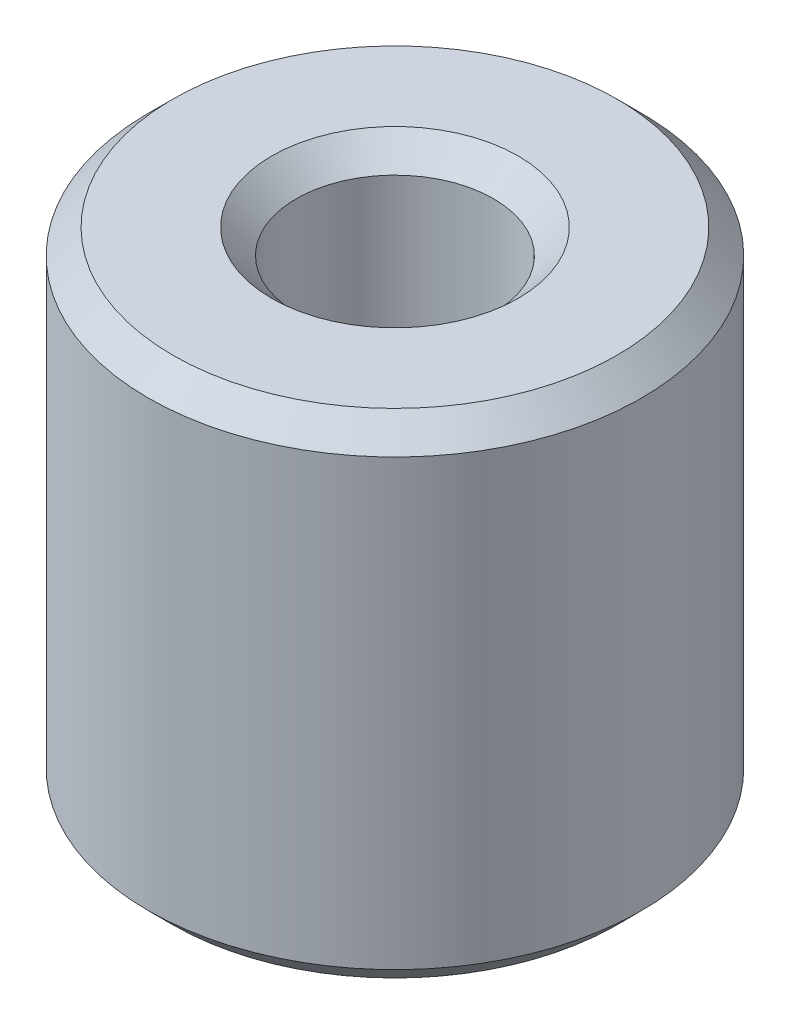
SolidWorks part; units mm, degrees
ref_plane "Front" through (0, 0, 0) normal (0, 0, 1) x (1, 0, 0)
ref_plane "Top" through (0, 0, 0) normal (0, 1, 0) x (1, 0, 0)
ref_plane "Right" through (0, 0, 0) normal (1, 0, 0) x (0, 0, -1)
sketch "Sketch1" plane through (0, 0, 0) normal (0, 1, 0) x (1, 0, 0)
  circle A0 centre (0, 0) radius 4
  circle A1 centre (0, 0) radius 1.6
  dimension "D1" = 8
  dimension "D2" = 3.2
extrude "Boss-Extrude1" add sketch "Sketch1" along normal blind 8
chamfer "Chamfer1" distance 0.4 angle 45 4 edges at (0, 0, 1.6) (0, 0, 4) (0, 8, 1.6) (0, 8, 4)
